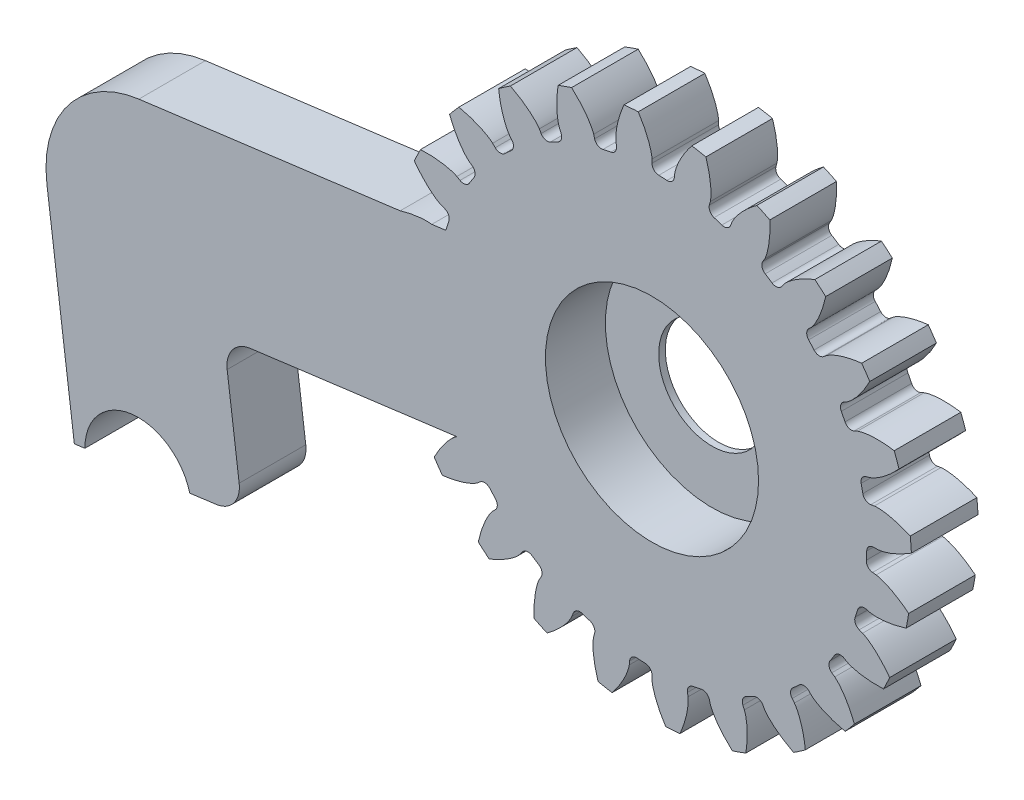
SolidWorks part; units mm, degrees
ref_plane "前视基准面" through (0, 0, 0) normal (0, 0, 1) x (1, 0, 0)
ref_plane "上视基准面" through (0, 0, 0) normal (0, 1, 0) x (1, 0, 0)
ref_plane "右视基准面" through (0, 0, 0) normal (1, 0, 0) x (0, 0, -1)
sketch "草图1" plane through (0, 0, 0) normal (0, 0, 1) x (1, 0, 0)
  circle A0 centre (0, 0) radius 19.5
  dimension "D1" = 39
extrude "凸台-拉伸1" add sketch "草图1" along normal mid plane 5
sketch "草图4" plane through (0, 0, 0) normal (0, 0, 1) x (1, 0, 0)
  line L1 (0, 0) -> (23.8901, -1.2086) construction
  line L2 (16.9145, 0) -> (16.125, 0)
  line L3 (16.8281, -1.707) -> (16.0427, -1.6273)
  arc A1 (17.998, 0.2683) -> (17.977, -0.9094) centre (0, 0) cw construction
  arc A3 (23.372, 5.0941) -> (22.7385, -7.4268) centre (0, 0) cw
  arc A4 (16.0427, -1.6273) -> (16.125, 0) centre (0, 0) ccw
  spline S0 degree 4 poles (16.8281, -1.707) (16.8405, -1.7085) (16.8752, -1.7136) (16.9404, -1.7264) (17.0458, -1.7519) (17.1786, -1.7908) (17.3482, -1.8487) (17.545, -1.9264) (17.7579, -2.0215) (17.9853, -2.1355) (18.2084, -2.2583) (18.4269, -2.3892) (18.6409, -2.527) (18.8954, -2.7025) (19.194, -2.9248) (19.5326, -3.2014) (19.9037, -3.5346) (20.2673, -3.8941) (20.6127, -4.264) (20.9467, -4.6555) (21.259, -5.0467) (21.567, -5.4702) (21.843, -5.8697) (22.1332, -6.3351) (22.3619, -6.716) (22.6425, -7.2361) (22.8019, -7.5485) (22.981, -7.9199) (23.0566, -8.0879) (23.1032, -8.1912) knots 0 0 0 0 0 0.005377 0.015084 0.028532 0.04661 0.064855 0.092111 0.119476 0.146842 0.174209 0.201575 0.228941 0.256307 0.307035 0.361767 0.4165 0.471232 0.525964 0.580697 0.635429 0.690161 0.744894 0.799626 0.854358 0.909091 0.954545 1 1 1 1 1 construction
  spline S1 degree 4 poles (16.8281, -1.707) (16.8405, -1.7085) (16.8752, -1.7136) (16.9404, -1.7264) (17.0458, -1.7519) (17.1786, -1.7908) (17.3482, -1.8487) (17.545, -1.9264) (17.7579, -2.0215) (17.9853, -2.1355) (18.2084, -2.2583) (18.4269, -2.3892) (18.6409, -2.527) (18.8954, -2.7025) (19.194, -2.9248) (19.5326, -3.2014) (19.9037, -3.5346) (20.2673, -3.8941) (20.6127, -4.264) (20.9467, -4.6555) (21.259, -5.0467) (21.567, -5.4702) (21.843, -5.8697) (22.1332, -6.3351) (22.3619, -6.716) (22.5816, -7.1233) (22.6862, -7.3236) (22.7386, -7.4268) knots 0 0 0 0 0 0.005377 0.015084 0.028532 0.04661 0.064855 0.092111 0.119476 0.146842 0.174209 0.201575 0.228941 0.256307 0.307035 0.361767 0.4165 0.471232 0.525964 0.580697 0.635429 0.690161 0.744894 0.799626 0.854358 0.909089 0.909089 0.909089 0.909089 0.909089
  spline S2 degree 4 poles (16.9145, 0) (16.927, 0.0003) (16.962, 0.0018) (17.0281, 0.008) (17.1356, 0.0227) (17.2716, 0.0481) (17.4462, 0.0885) (17.6498, 0.1459) (17.8712, 0.2191) (18.109, 0.3096) (18.3433, 0.4092) (18.5739, 0.5174) (18.8007, 0.6329) (19.0717, 0.7818) (19.3912, 0.9728) (19.7559, 1.2138) (20.1588, 1.5079) (20.5568, 1.8288) (20.9378, 2.162) (21.3096, 2.5178) (21.6598, 2.8755) (22.0089, 3.2657) (22.3239, 3.6354) (22.6595, 4.0691) (22.9254, 4.4249) (23.2571, 4.9141) (23.4473, 5.2088) (23.6629, 5.5603) (23.7551, 5.7197) (23.8119, 5.8178) knots 0 0 0 0 0 0.005377 0.015084 0.028532 0.04661 0.064855 0.092111 0.119476 0.146842 0.174209 0.201575 0.228941 0.256307 0.307035 0.361767 0.4165 0.471232 0.525964 0.580697 0.635429 0.690161 0.744894 0.799626 0.854358 0.909091 0.954545 1 1 1 1 1 construction
  spline S3 degree 4 poles (16.9145, 0) (16.927, 0.0003) (16.962, 0.0018) (17.0281, 0.008) (17.1356, 0.0227) (17.2716, 0.0481) (17.4462, 0.0885) (17.6498, 0.1459) (17.8712, 0.2191) (18.109, 0.3096) (18.3433, 0.4092) (18.5739, 0.5174) (18.8007, 0.6329) (19.0717, 0.7818) (19.3912, 0.9728) (19.7559, 1.2138) (20.1588, 1.5079) (20.5568, 1.8288) (20.9378, 2.162) (21.3096, 2.5178) (21.6598, 2.8755) (22.0089, 3.2657) (22.3239, 3.6354) (22.6595, 4.0691) (22.9254, 4.4249) (23.1852, 4.808) (23.3094, 4.9967) (23.372, 5.0941) knots 0 0 0 0 0 0.005377 0.015084 0.028532 0.04661 0.064855 0.092111 0.119476 0.146842 0.174209 0.201575 0.228941 0.256307 0.307035 0.361767 0.4165 0.471232 0.525964 0.580697 0.635429 0.690161 0.744894 0.799626 0.854358 0.909091 0.909091 0.909091 0.909091 0.909091
  dimension "D1" = 18
  dimension "D3" = 32.25
  dimension "D2" = 1.1781
ref_plane "基准面2" through (0, 0, 0) normal (-0.0505, -0.9987, 0) x (0.9987, -0.0505, 0)
extrude "切除-拉伸1" cut sketch "草图4" against normal through all both and the other way through all
fillet "圆角1" radius 0.525 2 edges at (16.0427, -1.6273, 0) (16.125, 0, 0)
pattern_circular "阵列(圆周)1" count 24 over 360 about axis through (0, 0, 2.5) along (0, 0, -1) of "切除-拉伸1", "圆角1"
sketch "草图5" plane through (0, 0, 0) normal (0, 0, 1) x (1, 0, 0)
  line L1 (-3, 0) -> (3, 0)
  line L2 (-3, 0) -> (-3, -10.8)
  line L3 (-3, -10.8) -> (3, -10.8)
  line L4 (3, 0) -> (3, -10.8)
  line L5 (-3, 0) -> (3, -10.8) construction
  line L6 (-3, -10.8) -> (3, 0) construction
  circle A0 centre (0, 0) radius 9
  point P3 (0, -5.4)
  dimension "D1" = 18
  dimension "D2" = 19.8
  dimension "D3" = 6
extrude "切除-拉伸2" [suppressed] cut sketch "草图5" against normal through all both and the other way through all contours A0 L2 L3 L4
sketch "草图6" plane through (0, 0, 2.5) normal (0, 0, 1) x (1, 0, 0)
  circle A0 centre (0, 0) radius 18 construction
  dimension "D1" = 36
sketch "草图7" plane through (0, 0, 2.5) normal (0, 0, 1) x (1, 0, 0)
  circle A0 centre (0, 0) radius 1.25
  dimension "D1" = 2.5
extrude "切除-拉伸3" cut sketch "草图7" against normal blind 10
sketch "草图8" plane through (0, 0, 2.5) normal (0, 0, 1) x (1, 0, 0)
  circle A0 centre (0, 0) radius 8
  dimension "D1" = 16
extrude "切除-拉伸4" cut sketch "草图8" against normal blind 4.5
sketch "草图9" plane through (0, 0, -2) normal (0, 0, 1) x (1, 0, 0)
  circle A0 centre (0, 0) radius 4
  dimension "D1" = 8
extrude "切除-拉伸5" cut sketch "草图9" against normal blind 4
sketch "草图10" plane through (0, 0, 2.5) normal (0, 0, 1) x (1, 0, 0)
  line L0 (2.3183, -17.8501) -> (-53.791, -25.1374) construction
  line L1 (-0.7206, 0) -> (-40.4437, -5.1591) construction
  line L5 (-44.7797, -12.3705) -> (-43.363, -23.2788)
  line L16 (-14.7206, 4.6427) -> (-46.454, 0.5213)
  line L17 (-14.7206, 4.6427) -> (-13.0462, -8.249)
  line L18 (-13.0462, -8.249) -> (-32.1485, -10.73)
  line L19 (-46.454, 0.5213) -> (-44.7797, -12.3705)
  line L20 (-43.363, -23.2788) -> (-42.5696, -23.1758)
  line L21 (-34.6985, -22.1535) -> (-30.7318, -21.6383)
  line L22 (-30.7318, -21.6383) -> (-32.1485, -10.73)
  circle A1 centre (0, 0) radius 3.1249 construction
  arc A3 (-34.6985, -22.1535) -> (-42.5696, -23.1758) centre (-38.5696, -23.1605) ccw
  dimension "D4" = 11
  dimension "D7" = 4
  dimension "D1" = 32
  dimension "D2" = 14
  dimension "D3" = 13
  dimension "D5" = 0.5
  dimension "D6" = 0.8
  dimension "D8" = 4
  dimension "D9" = 13
extrude "凸台-拉伸2" add sketch "草图10" against normal up to surface (5 mm away) up to face at (4, 0, -2.5)
fillet "圆角2" radius 2 1 edges at (-32.1485, -10.73, 0)
fillet "圆角3" radius 2 1 edges at (-30.7318, -21.6383, 0)
fillet "圆角4" radius 8 1 edges at (-46.454, 0.5213, 0)
equation "\"D1@草图1\" = \"da\""
equation "\"D1@凸台-拉伸1\"=\"b\""
equation "\"b\"= 5'齿轮宽度"
equation "\"m\"= 1.5mm'模数"
equation "\"z\"= 24'齿数"
equation "\"x\"= 0'变位系数"
equation "\"pz\"= pi * \"m\"'导程"
equation "\"ha*\"= 1'齿顶高系数"
equation "\"c*\"= 0.25'顶隙系数"
equation "\"d2\"= \"m\" * \"z\"'分度圆"
equation "\"alfa\"= 20'压力角"
equation "\"db\"= \"d2\" * cos ( \"alfa\" )'基圆"
equation "\"df\"= \"d2\" - 2 * ( \"ha*\" + \"c*\" - \"x\" ) * \"m\"'齿根圆"
equation "\"D1@草图4\"=\"d2\"/2"
equation "\"D2@草图4\"=\"pz\"/4"
equation "\"D1@阵列(圆周)1\"=\"z\""
equation "\"D3@草图4\"=\"df\""
equation "\"da\"= \"d2\" + 2 * ( \"ha*\" + \"x\" ) * \"m\"'齿顶圆"
equation "\"c\"= \"m\" * 0.35'齿根圆角"
equation "\"D1@圆角1\"=\"c\""
equation "\"dh\"= 18'内孔直径"
equation "\"h\"= 19.8'槽深"
equation "\"D1@草图5\"=\"dh\""
equation "\"D2@草图5\"=\"h\""
equation "\"k\"= 6'槽宽"
equation "\"D1@草图6\"=\"d2\""
